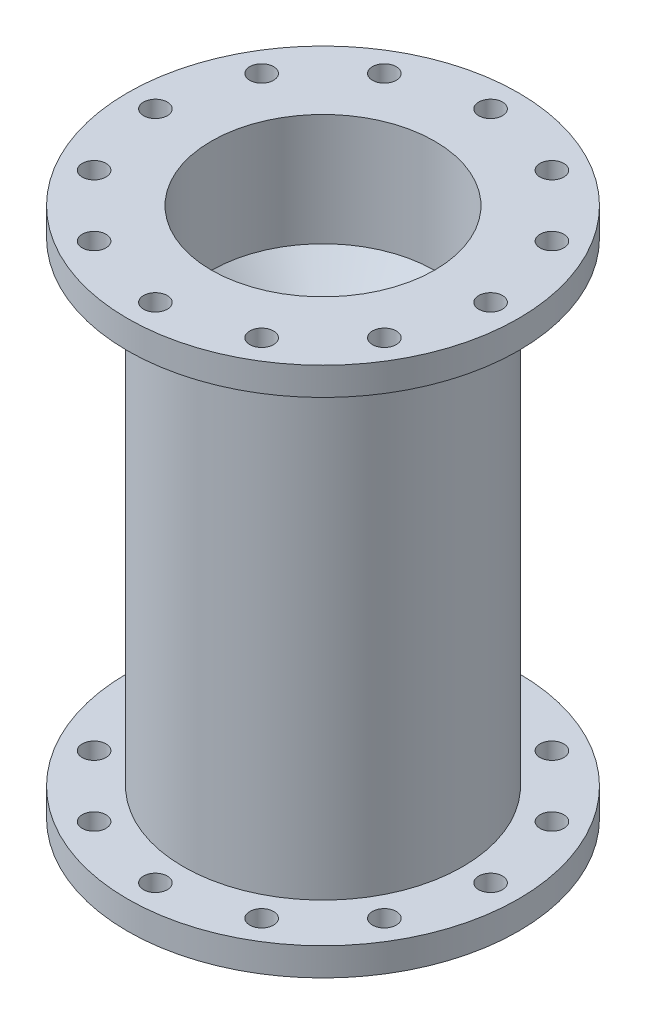
SolidWorks part; units mm, degrees
ref_plane "Front Plane" through (0, 0, 0) normal (0, 0, 1) x (1, 0, 0)
ref_plane "Top Plane" through (0, 0, 0) normal (0, 1, 0) x (1, 0, 0)
ref_plane "Right Plane" through (0, 0, 0) normal (1, 0, 0) x (0, 0, -1)
sketch "Sketch1" plane through (0, 0, 0) normal (1, 0, 0) x (0, 0, -1)
  line L1 (31.75, 6.35) -> (31.75, 114.3)
  line L8 (31.75, 120.65) -> (44.45, 120.65)
  line L9 (44.45, 120.65) -> (44.45, 114.3)
  line L10 (44.45, 114.3) -> (31.75, 114.3)
  line L11 (31.75, 0) -> (44.45, 0)
  line L12 (44.45, 0) -> (44.45, 6.35)
  line L13 (44.45, 6.35) -> (31.75, 6.35)
  line L27 (25.4, 114.3) -> (25.4, 120.65)
  line L28 (25.4, 120.65) -> (31.75, 120.65)
  line L29 (25.4, 6.35) -> (25.4, 0)
  line L30 (25.4, 0) -> (31.75, 0)
  line L31 (25.4, 114.3) -> (25.4, 6.35)
  line L32 (25.4, 0) -> (0, 0) construction
  line L33 (0, 0) -> (0, 6.35) construction
  dimension "D1" = 6.35
  dimension "D2" = 6.35
  dimension "D3" = 12.7
  dimension "D4" = 12.7
  dimension "D5" = 12.7
  dimension "D6" = 12.7
  dimension "D7" = 107.95
  dimension "D8" = 25.4
  dimension "D9" = 6.35
revolve "Chamber" add sketch "Sketch1" angle 360 about L33
sketch "Sketch4" plane through (0, 0, 0) normal (1, 0, 0) x (0, 0, -1)
  line L0 (0, 0) -> (0, 120.65) construction
  line L1 (25.4, 120.65) -> (-25.4, 120.65) construction
  line L8 (0, 60.325) -> (25.4, 60.325) construction
  line L15 (0, 0) -> (25.4, 0) construction
  line L16 (25.4, 0) -> (25.4, 92.6437) construction
  line L17 (25.4, 95.1837) -> (7.62, 95.1837) construction
  line L18 (7.62, 95.1837) -> (7.62, 77.4037) construction
  line L22 (25.4, 92.6437) -> (25.4, 95.1837)
  line L23 (25.4, 95.1837) -> (7.62, 77.4037)
  line L24 (7.62, 77.4037) -> (7.62, 74.8637)
  line L25 (7.62, 74.8637) -> (25.4, 92.6437)
  line L26 (25.4, 95.1837) -> (25.4662, 120.5836) construction
  line L27 (0, 120.65) -> (25.4662, 120.5836) construction
  dimension "D2" = 25.4
  dimension "D1" = 7.62
  dimension "D4" = 2.54
  dimension "D3" = 25.4
revolve "Turbulence Rings" add sketch "Sketch4" angle 360 about L0
sketch "Sketch5" plane through (0, 120.65, 0) normal (0, 1, 0) x (1, 0, 0)
  line L0 (0, 0) -> (-38.1, 0) construction
  line L1 (0, 0) -> (-32.9956, 19.05) construction
  circle A0 centre (0, 0) radius 38.1 construction
  point P0 (0, 0)
  point P5 (-38.1, 0)
  point P9 (-32.9956, 19.05)
  point P10 (-19.05, 32.9956)
  point P11 (0, 38.1)
  point P12 (19.05, 32.9956)
  point P13 (32.9956, 19.05)
  point P14 (38.1, 0)
  point P15 (32.9956, -19.05)
  point P16 (19.05, -32.9956)
  point P17 (0, -38.1)
  point P18 (-19.05, -32.9956)
  point P19 (-32.9956, -19.05)
  point P20 (0, 0)
  point P21 (0, 0)
  point P24 (0, 0)
  point P26 (0, 0)
  dimension "D3" = 38.1
  dimension "D1" = 30
  dimension "D2" = 12
hole_wizard "#3 (0.213) Diameter Hole3" positions "Sketch5" profile "Sketch9" hole size "#3" standard "ANSI Inch" end condition through all
sketch "Sketch9" plane through (0, 120.65, 0) normal (1, 0, 0) x (0, 0, 1)
  line L0 (0, 0) -> (0, 120.65)
  line L1 (0, 120.65) -> (2.7051, 120.65)
  line L2 (2.7051, 120.65) -> (2.7051, 0)
  line L5 (2.7051, 0) -> (0, 0)
  line L11 (0, -6.35) -> (0, 107.95) construction
  dimension "Thru Hole Dia." = 5.4102
  dimension "Thru Hole Depth" = 120.65
equation "\"Thickness of Material\"= 0.3in"
equation "\"Chamber Length\"= 4.25in"
equation "\"Flange Length\"= 0.5in"
equation "\"Chamber Wall Thickness\"= 0.25in"
equation "\"Ring Length\"= 1.2in"
equation "\"Ring Thickness\"= 0.1in"
equation "\"Number of Rings\"= 2"
equation "\"Chamber Radius\"= 1in"
equation "\"D7@Sketch1\"= \"Chamber Length\""
equation "\"D9@Sketch1\"= \"Chamber Wall Thickness\""
equation "\"D8@Sketch1\"= \"Chamber Radius\""
equation "\"Flange Thickness\"= 0.25in"
equation "\"D1@Sketch1\"= \"Flange Thickness\""
equation "\"D3@Sketch5\"= \"Chamber Radius\" + \"Chamber Wall Thickness\" + ( \"Flange to Inner Wall Length\" / 2 )"
equation "\"Flange to Inner Wall Length\"= ( \"Chamber Radius\" + \"Chamber Wall Thickness\" + \"Flange Length\" ) - ( \"Chamber Radius\" + \"Chamber Wall Thickness\" )"
equation "\"D2@Sketch4\"= \"Chamber Radius\""
equation "\"Turbulence Ring Distance from Top\"= 1in"
equation "\"D4@Sketch1\"= \"Flange Length\""
equation "\"D3@Sketch1\"= \"Flange Length\""
equation "\"D5@Sketch1\"= \"Flange Length\""
equation "\"D6@Sketch1\"= \"Flange Length\""
equation "\"Center to Ring Edge Distance\"= 0.3 * ( \"Chamber Radius\" )"
equation "\"D1@Sketch4\"= \"Center to Ring Edge Distance\""
equation "\"D4@Sketch4\"= \"Ring Thickness\""
equation "\"D3@Sketch4\"= \"Turbulence Ring Distance from Top\""
